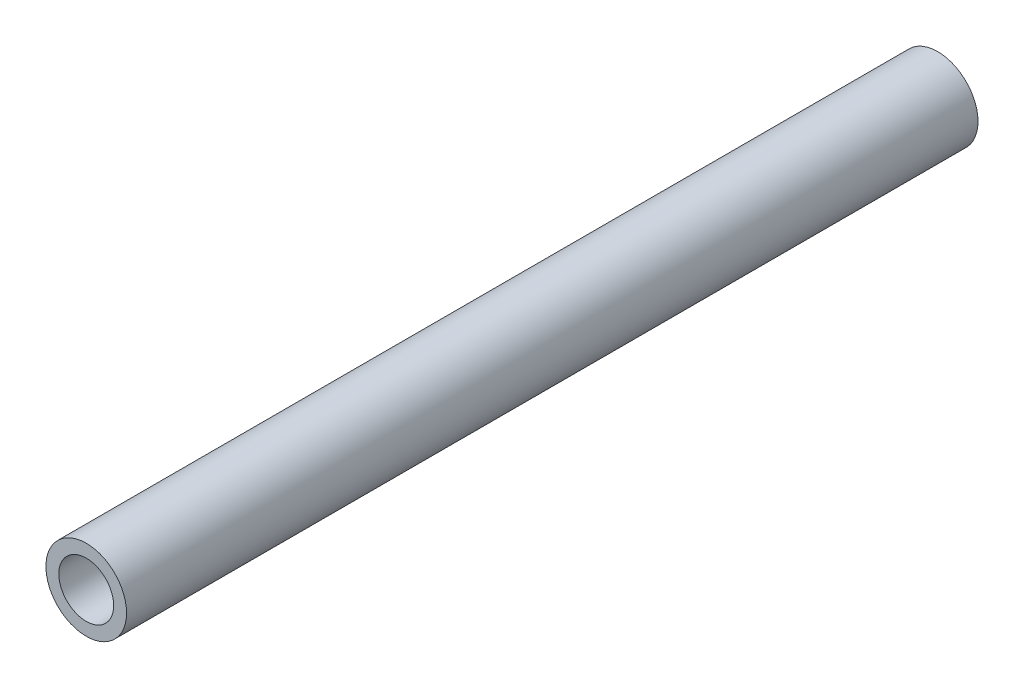
SolidWorks part; units mm, degrees
ref_plane "Front Plane" through (0, 0, 0) normal (0, 0, 1) x (1, 0, 0)
ref_plane "Top Plane" through (0, 0, 0) normal (0, 1, 0) x (1, 0, 0)
ref_plane "Right Plane" through (0, 0, 0) normal (1, 0, 0) x (0, 0, -1)
sketch "Sketch3" plane through (0, 0, 0) normal (0, 0, 1) x (1, 0, 0)
  circle A0 centre (-29.5998, 13.8633) radius 4.25
  circle A1 centre (-29.5998, 13.8633) radius 6.25
extrude "Boss-Extrude2" add sketch "Sketch3" along normal blind 132
